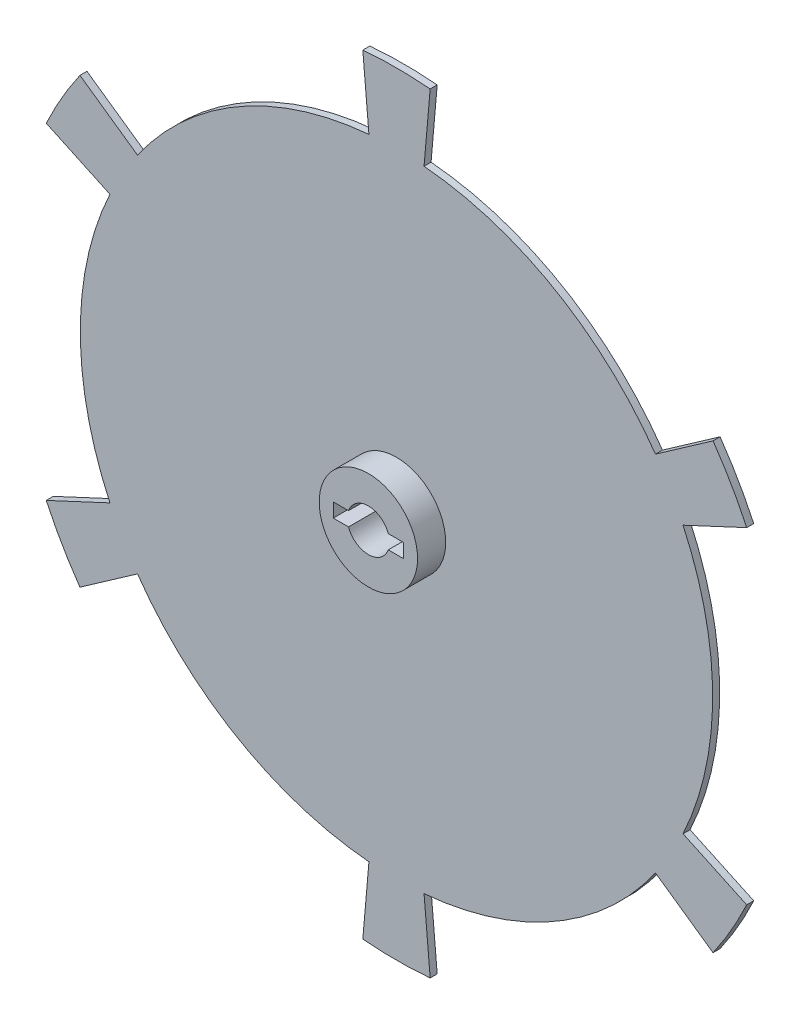
SolidWorks part; units mm, degrees
ref_plane "Front" through (0, 0, 0) normal (0, 0, 1) x (1, 0, 0)
ref_plane "Top" through (0, 0, 0) normal (0, 1, 0) x (1, 0, 0)
ref_plane "Right" through (0, 0, 0) normal (1, 0, 0) x (0, 0, -1)
sketch "Sketch1" plane through (0, 0, 0) normal (0, 0, 1) x (1, 0, 0)
  line L0 (28.2843, -10) -> (50, -10)
  line L1 (-50, 10) -> (-28.2843, 10)
  line L2 (-50, 10) -> (-50, -10)
  line L3 (-50, -10) -> (-28.2843, -10)
  line L4 (50, 10) -> (50, -10)
  line L5 (28.2843, 10) -> (50, 10)
  circle A0 centre (0, 0) radius 450
  arc A1 (28.2843, 10) -> (-28.2843, 10) centre (0, 0) ccw
  arc A2 (-28.2843, -10) -> (28.2843, -10) centre (0, 0) ccw
extrude "Boss-Extrude1" add sketch "Sketch1" along normal blind 10
sketch "Sketch2" plane through (0, 0, 10) normal (0, 0, 1) x (1, 0, 0)
  line L0 (-50, 10) -> (-50, -10)
  line L1 (-50, -10) -> (-28.2843, -10)
  line L2 (-50, 10) -> (-28.2843, 10)
  line L3 (28.2843, 10) -> (50, 10)
  line L4 (50, 10) -> (50, -10)
  line L5 (50, -10) -> (28.2843, -10)
  circle A0 centre (0, 0) radius 70
  arc A1 (-28.2843, -10) -> (28.2843, -10) centre (0, 0) ccw
  arc A2 (28.2843, 10) -> (-28.2843, 10) centre (0, 0) ccw
extrude "Boss-Extrude2" add sketch "Sketch2" along normal blind 40
sketch "Sketch3" plane through (0, 0, 10) normal (0, 0, 1) x (1, 0, 0)
  line L0 (0, 0) -> (-47.9357, 547.9071)
  line L1 (47.9357, 547.9071) -> (0, 0)
  line L2 (0, 0) -> (450.5336, 315.467)
  line L3 (498.4693, 232.44) -> (0, 0)
  line L4 (0, 0) -> (498.4693, -232.44)
  line L5 (450.5336, -315.467) -> (0, 0)
  line L6 (0, 0) -> (47.9357, -547.9071)
  line L7 (-47.9357, -547.9071) -> (0, 0)
  line L8 (0, 0) -> (-450.5336, -315.467)
  line L9 (-498.4693, -232.44) -> (0, 0)
  line L10 (0, 0) -> (-498.4693, 232.44)
  line L11 (-450.5336, 315.467) -> (0, 0)
  line L12 (0, 0) -> (0, 450)
  arc A0 (-47.9357, 547.9071) -> (47.9357, 547.9071) centre (0, 0) cw
  arc A1 (450.5336, 315.467) -> (498.4693, 232.44) centre (0, 0) cw
  arc A2 (498.4693, -232.44) -> (450.5336, -315.467) centre (0, 0) cw
  arc A3 (47.9357, -547.9071) -> (-47.9357, -547.9071) centre (0, 0) cw
  arc A4 (-450.5336, -315.467) -> (-498.4693, -232.44) centre (0, 0) cw
  arc A5 (-498.4693, 232.44) -> (-450.5336, 315.467) centre (0, 0) cw
  circle A6 centre (0, 0) radius 400
  circle M1 centre (0, 0) radius 450
extrude "Boss-Extrude3" add sketch "Sketch3" along direction (0, 0, 1) on the side against the normal up to surface (10 mm away) contours A5 L10 L11 M1 | A0 L0 L1 M1 | A1 L2 L3 M1 | A2 L4 L5 M1 | A3 L6 L7 M1 | A4 L8 L9 M1
